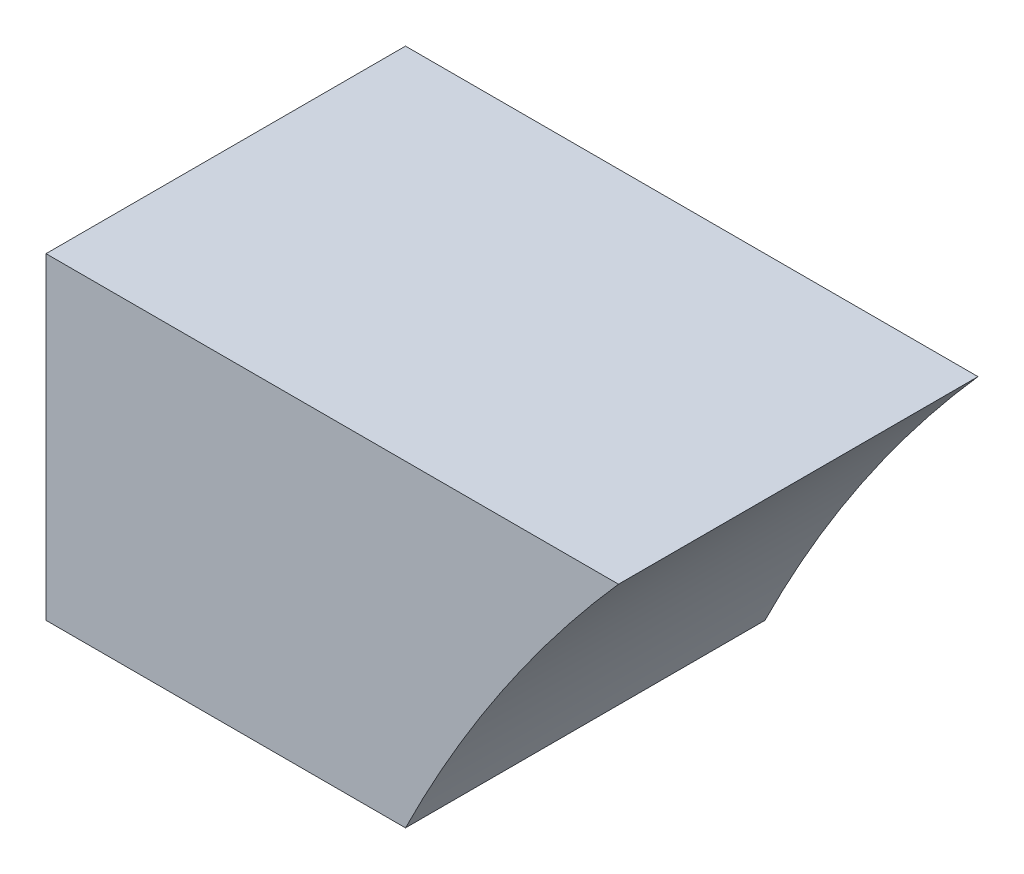
SolidWorks part; units mm, degrees
material "砖"
ref_plane "前视基准面" through (0, 0, 0) normal (0, 0, 1) x (1, 0, 0)
ref_plane "上视基准面" through (0, 0, 0) normal (0, 1, 0) x (1, 0, 0)
ref_plane "右视基准面" through (0, 0, 0) normal (1, 0, 0) x (0, 0, -1)
sketch "草图1" plane through (0, 0, 0) normal (0, 0, 1) x (1, 0, 0)
  line L0 (-4560, 0) -> (-7920, 0)
  line L1 (-12480, 7680) -> (0, 7680)
  line L2 (-12480, 7680) -> (-12480, 0)
  line L3 (-12480, 0) -> (0, 0)
  line L4 (0, 7680) -> (0, 0)
  line L5 (-7920, 0) -> (-7920, 3840)
  line L6 (-7920, 3840) -> (-4560, 3840)
  line L7 (-4560, 3840) -> (-4560, 0)
  line L8 (-7920, 3840) -> (-8160, 3840)
  line L9 (-4560, 3840) -> (-4320, 3840)
  line L10 (-7837.7749, 4359.1486) -> (-8066.0285, 4433.3126)
  line L11 (-7599.1486, 4827.4792) -> (-7793.3126, 4968.5477)
  line L12 (-7227.4792, 5199.1486) -> (-7368.5477, 5393.3126)
  line L13 (-6759.1486, 5437.7749) -> (-6833.3126, 5666.0285)
  line L14 (-6240, 5520) -> (-6240, 5760)
  line L15 (-5720.8514, 5437.7749) -> (-5646.6874, 5666.0285)
  line L16 (-5252.5208, 5199.1486) -> (-5111.4523, 5393.3126)
  line L17 (-4880.8514, 4827.4792) -> (-4686.6874, 4968.5477)
  line L18 (-4642.2251, 4359.1486) -> (-4413.9715, 4433.3126)
  line L19 (-4560, 3840) -> (-4320, 3840)
  line L20 (-4573.7633, 3298.6069) -> (-4560, 3294.1349)
  line L21 (-6833.3126, 5666.0285) -> (-6928.8298, 5960)
  line L22 (-5683.7694, 5551.9017) -> (-5551.1702, 5960)
  line L23 (-5551.1702, 5960) -> (-6928.8298, 5960)
  line L24 (-7920, 0) -> (-9123.3069, 0)
  line L25 (-8160, 0) -> (-8640, 0)
  line L26 (-8160, 0) -> (-8640, 0)
  line L27 (-8640, 3840) -> (-8160, 3840)
  line L28 (-8640, 3840) -> (-8640, 4264)
  line L29 (-7837.7749, 3320.8514) -> (-7920, 3294.1349) [skipped]
  line L30 (-7599.1486, 2852.5208) -> (-7793.3126, 2711.4523) [skipped]
  line L31 (-7227.4792, 2480.8514) -> (-7368.5477, 2286.6874) [skipped]
  line L32 (-6759.1486, 2242.2251) -> (-6833.3126, 2013.9715) [skipped]
  line L33 (-6240, 2160) -> (-6240, 1920) [skipped]
  line L34 (-5720.8514, 2242.2251) -> (-5646.6874, 2013.9715) [skipped]
  line L35 (-5252.5208, 2480.8514) -> (-5111.4523, 2286.6874) [skipped]
  line L36 (-4880.8514, 2852.5208) -> (-4686.6874, 2711.4523) [skipped]
  line L37 (-8640, 4264) -> (-8112.5982, 4264)
  line L38 (-8112.5982, 4264) -> (-8592.5982, 4264)
  line L39 (-8592.5982, 4264) -> (-8592.5982, 4688)
  line L40 (-8592.5982, 4688) -> (-7962.5841, 4688)
  line L41 (-7962.5841, 4688) -> (-8442.5841, 4688)
  line L42 (-8442.5841, 4688) -> (-8442.5841, 5112)
  line L43 (-8442.5841, 5112) -> (-7678.1989, 5112)
  line L44 (-7678.1989, 5112) -> (-8158.1989, 5112)
  line L45 (-8158.1989, 5112) -> (-8158.1989, 5536)
  line L46 (-8158.1989, 5536) -> (-7139.9911, 5536)
  line L47 (-7139.9911, 5536) -> (-7619.9911, 5536)
  line L48 (-7619.9911, 5536) -> (-7619.9911, 5960)
  line L49 (-7619.9911, 5960) -> (-6928.8298, 5960)
  arc A0 (-4560, 3840) -> (-7920, 3840) centre (-6240, 3840) ccw
  arc A1 (-4320, 3840) -> (-8160, 3840) centre (-6240, 3840) ccw
  point P7 (-6240, 0)
  point P56 (-6240, 3840)
  dimension "D5" = 3840
  dimension "D1" = 12480
  dimension "D2" = 7680
  dimension "D3" = 3360
  dimension "D4" = 3840
  dimension "D7" = 240
  dimension "D8" = 480
  dimension "D9" = 424
  dimension "D10" = 720
  dimension "D11" = 480
  dimension "D12" = 480
  dimension "D13" = 480
  dimension "D14" = 480
  dimension "D6" = 20
extrude "凸台-拉伸1" add sketch "草图1" along normal blind 480 contours A1 L43 L42 L40
scale "缩放比例1" scale about origin uniform scaling yes scale factor 1.3
